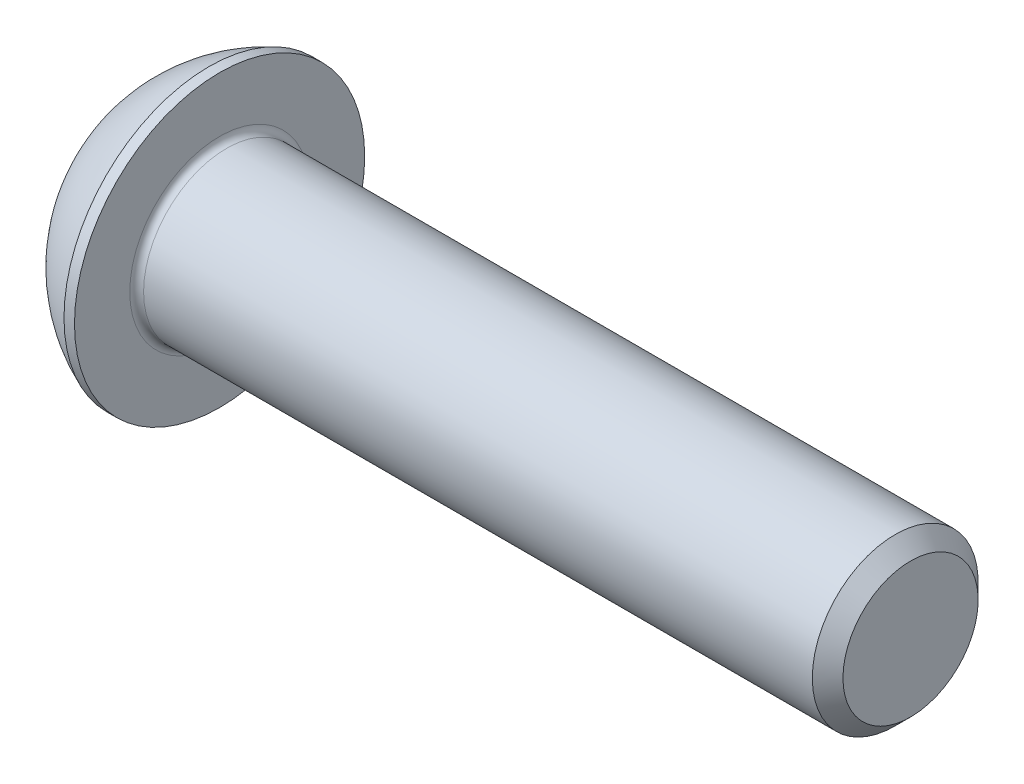
SolidWorks part; units mm, degrees
ref_plane "Plane1" through (0, 0, 0) normal (0, 0, 1) x (1, 0, 0)
ref_plane "Plane2" through (0, 0, 0) normal (0, 1, 0) x (1, 0, 0)
ref_plane "Plane3" through (0, 0, 0) normal (1, 0, 0) x (0, 0, -1)
sketch "BodySke" plane through (0, 0, 0) normal (0, 0, 1) x (1, 0, 0)
  line L0 (28.3, 0) -> (28.3, 2.4455)
  line L1 (27.7455, 3) -> (3.3, 3)
  line L2 (3.3, 3) -> (3.3, 5.25)
  line L3 (3.3, 5.25) -> (2.92, 5.25)
  line L4 (0, 0) -> (101.6, 0) construction
  line L5 (3.3, -5.25) -> (2.92, -5.25) construction
  line L6 (55.6768, -3) -> (3.3, -3) construction
  line L7 (28.3, 0) -> (0, 0)
  line L8 (0, 2.625) -> (0, -2.625) construction
  line L9 (0, 0) -> (0, 2.625)
  line L10 (28.3, 2.4455) -> (27.7455, 3)
  line L11 (28.3, -2.4455) -> (27.7455, -3) construction
  line L12 (4.3, 9.525) -> (4.3, -3) construction
  line L13 (3.3, 9.525) -> (3.3, -3) construction
  arc A1 (0, 2.625) -> (2.92, 5.25) centre (4.9997, 0) cw
  dimension "D1" = 5.25
  dimension "Diameter" = 6
  dimension "Length" = 25
  dimension "Head_dia" = 10.5
  dimension "Head_ht" = 3.3
  dimension "Head_side_ht" = 0.38
  dimension "Minor_dia" = 4.891
  dimension "Body_ch_ang" = 45
  dimension "Advance" = 1
  dimension "Thread_nom" = 25
revolve "BaseBody" add sketch "BodySke" angle 360 about L4
cosmetic thread "ThreadCosmetic" [suppressed] parameters "Thread_length"=23, "Thread_minor"=4.891
fillet "Fillet1" radius 0.25 1 edges at (3.3, 0, 3)
sketch "Sketch2" plane through (0, 0, 0) normal (0, 0, 1) x (1, 0, 0)
  line L0 (0, 2) -> (2.08, 2)
  line L1 (2.08, 2) -> (3.2347, 0)
  line L3 (3.2347, 0) -> (0, 0)
  line L4 (0, 0) -> (0, 2)
  line L5 (0, -2) -> (2.08, -2) construction
  line L6 (0, 0) -> (47.625, 0) construction
  dimension "D2" = 60
  dimension "PreBroach_depth" = 2.08
  dimension "PreBroach_dia" = 4
revolve "PreBroach" cut sketch "Sketch2" angle 360 about L6
sketch "Sketch3" plane through (0, 0, 0) normal (1, 0, 0) x (0, 0, -1)
  line L0 (-2, -1.1547) -> (-2, 1.1547)
  line L1 (-2, 1.1547) -> (0, 2.3094)
  line L2 (0, 2.3094) -> (2, 1.1547)
  line L3 (2, 1.1547) -> (2, -1.1547)
  line L4 (2, -1.1547) -> (0, -2.3094)
  line L5 (0, -2.3094) -> (-2, -1.1547)
  dimension "D1" = 2
  dimension "D2" = 2
  dimension "D3" = 4
  dimension "Hex_size" = 4
extrude "Hex" cut sketch "Sketch3" along normal blind 2.08
sketch "ThdSchSke" [suppressed] plane through (0, 0, 0) normal (0, 0, 1) x (1, 0, 0)
  line L0 (12.8, -6.8985) -> (12.0287, -8)
  line L1 (12.8, -6.8985) -> (13.5713, -8)
  line L2 (13.5713, -8) -> (13.5713, -10)
  line L3 (-3.175, 0) -> (5.1513, 0) construction
  line L5 (13.5713, -10) -> (12.0287, -10)
  line L6 (12.0287, -10) -> (12.0287, -8)
  dimension "Thread_minor" = 4.891
  dimension "Diameter" = 6
  dimension "Start" = 5.3
  dimension "SideAngle" = 55
  dimension "VeeAngle" = 70
  dimension "Overcut" = 7.5
revolve "ThreadSchematic" [suppressed] cut sketch "ThdSchSke" angle 360 about L3
pattern_linear "ThdSchPat" [suppressed]
equation "\"D1@BodySke\" = \"Head_dia@BodySke\" * .5"
equation "\"Thread_minor@ThreadCosmetic\" = \"Minor_dia@BodySke\""
equation "\"D1@Sketch3\" = \"Hex_size@Sketch3\" / 2"
equation "\"D2@Sketch3\" = \"D1@Sketch3\""
equation "\"D3@Sketch3\" = \"Hex_size@Sketch3\""
equation "\"Thread_length@ThreadCosmetic\" = ((sgn( (\"Length@BodySke\" - \"Advance@BodySke\" * 2.0) - \"Thread_nom@BodySke\" )-1)*( (\"Length@BodySke\" - \"Advance@BodySke\" * 2.0) - \"Thread_nom@BodySke\" ))/-2+ \"Thread_nom@BodySke\""
equation "\"Thread_minor@ThdSchSke\" = \"Minor_dia@BodySke\""
equation "\"Diameter@ThdSchSke\" = \"Diameter@BodySke\""
equation "\"Overcut@ThdSchSke\" = \"Diameter@BodySke\" * 1.25"
equation "\"Start@ThdSchSke\" = \"Head_ht@BodySke\" + \"Length@BodySke\" - \"Thread_length@ThreadCosmetic\"  '---Non-countersunk---"
equation "\"Num_threads@ThdSchPat\" = int( \"Thread_length@ThreadCosmetic\" / \"Advance@BodySke\" + 0.999 )  + 1"
equation "\"Advance@ThdSchPat\" = \"Thread_length@ThreadCosmetic\" /  (\"Num_threads@ThdSchPat\" - 1) 'relax it"
equation "\"Num_threads@ThdSchPat\" = \"Num_threads@ThdSchPat\" - sgn( \"Num_threads@ThdSchPat\" - 1) '---chamfered tips only---"
